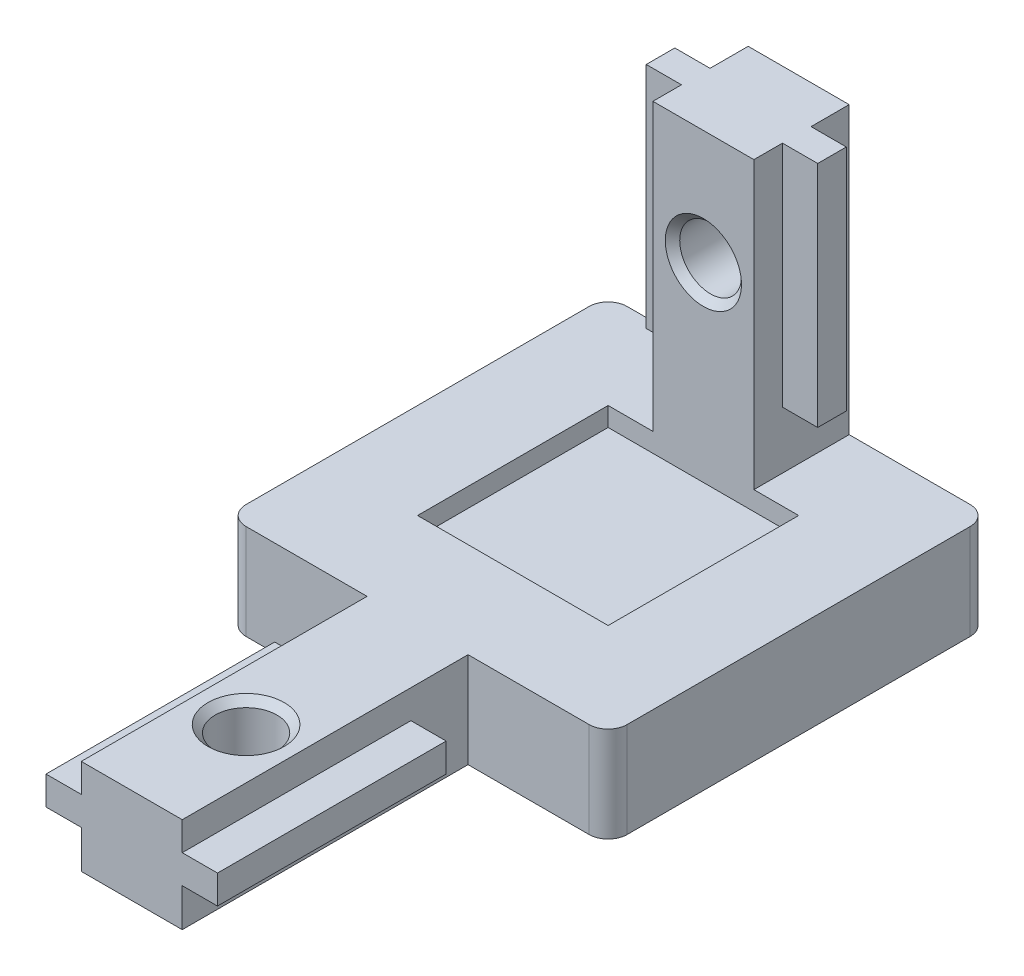
SolidWorks part; units mm, degrees
material "Stainless Steel (ferritic)"
ref_plane "Front Plane" through (0, 0, 0) normal (0, 0, 1) x (1, 0, 0)
ref_plane "Top Plane" through (0, 0, 0) normal (0, 1, 0) x (1, 0, 0)
ref_plane "Right Plane" through (0, 0, 0) normal (1, 0, 0) x (0, 0, -1)
ref_plane "Plane1" through (0, 5, 0) normal (0, 1, 0) x (1, 0, 0)
sketch "Sketch1" plane through (0, 5, 0) normal (0, 1, 0) x (1, 0, 0)
  line L0 (10, -35) -> (10, 0)
  line L1 (10, 0) -> (-10, 0)
  line L2 (-10, 0) -> (-10, -35)
  line L3 (-10, -35) -> (10, -35)
extrude "Boss-Extrude1" add sketch "Sketch1" against normal blind 5
sketch "Sketch2" plane through (0, 5, 0) normal (0, 1, 0) x (-1, 0, 0)
  line L0 (-2.65, 5) -> (2.65, 5)
  line L1 (2.65, 5) -> (2.65, 0)
  line L2 (2.65, 0) -> (-2.65, 0)
  line L3 (-2.65, 0) -> (-2.65, 5)
extrude "Boss-Extrude2" add sketch "Sketch2" along normal blind 15
sketch "Sketch3" plane through (0, 5, 0) normal (0, 1, 0) x (-1, 0, 0)
  line L0 (5, 15) -> (-5, 15)
  line L1 (-5, 15) -> (-5, 5)
  line L2 (-5, 5) -> (5, 5)
  line L3 (5, 5) -> (5, 15)
extrude "Cut-Extrude1" cut sketch "Sketch3" against normal blind 1
sketch "Sketch4" plane through (0, 0, 0) normal (0, -1, 0) x (1, 0, 0)
  line L0 (-10, 20) -> (-2.65, 20)
  line L1 (-2.65, 20) -> (-2.65, 35)
  line L2 (-2.65, 35) -> (-10, 35)
  line L3 (-10, 35) -> (-10, 20)
extrude "Cut-Extrude2" cut sketch "Sketch4" against normal through all
sketch "Sketch5" plane through (0, 0, 0) normal (0, -1, 0) x (1, 0, 0)
  line L0 (2.65, 35) -> (2.65, 20)
  line L1 (2.65, 20) -> (10, 20)
  line L2 (10, 20) -> (10, 35)
  line L3 (10, 35) -> (2.65, 35)
extrude "Cut-Extrude3" cut sketch "Sketch5" against normal through all
sketch "Sketch6" plane through (2.65, 0, 0) normal (1, 0, 0) x (0, 0, -1)
  line L0 (-2, 8) -> (-3.5, 8)
  line L1 (-3.5, 8) -> (-3.5, 20)
  line L2 (-3.5, 20) -> (-2, 20)
  line L3 (-2, 20) -> (-2, 8)
extrude "Boss-Extrude3" add sketch "Sketch6" along normal blind 1.85
sketch "Sketch7" plane through (-2.65, 0, 0) normal (-1, 0, 0) x (0, 0, 1)
  line L0 (3.5, 8) -> (2, 8)
  line L1 (2, 8) -> (2, 20)
  line L2 (2, 20) -> (3.5, 20)
  line L3 (3.5, 20) -> (3.5, 8)
extrude "Boss-Extrude4" add sketch "Sketch7" along normal blind 1.85
sketch "Sketch8" plane through (-2.65, 0, 0) normal (-1, 0, 0) x (0, 0, 1)
  line L0 (23, 2) -> (23, 3.5)
  line L1 (23, 3.5) -> (35, 3.5)
  line L2 (35, 3.5) -> (35, 2)
  line L3 (35, 2) -> (23, 2)
extrude "Boss-Extrude5" add sketch "Sketch8" along normal blind 1.85
sketch "Sketch9" plane through (2.65, 0, 0) normal (1, 0, 0) x (0, 0, -1)
  line L0 (-23, 3.5) -> (-23, 2)
  line L1 (-23, 2) -> (-35, 2)
  line L2 (-35, 2) -> (-35, 3.5)
  line L3 (-35, 3.5) -> (-23, 3.5)
extrude "Boss-Extrude6" add sketch "Sketch9" along normal blind 1.85
hole_wizard "M3 Clearance Hole1" positions "Sketch11" profile "Sketch10" hole size "M3" standard "ANSI Metric"
sketch "Sketch11" plane through (0, 0, 0) normal (0, -1, 0) x (-1, 0, 0)
  point P0 (0, -29)
sketch "Sketch10" plane through (0, 0, 29) normal (1, 0, 0) x (0, 0, -1)
  line L0 (0, 0) -> (0, 20)
  line L1 (0, 20) -> (1.621, 20)
  line L2 (1.621, 20) -> (1.621, 0)
  line L5 (1.621, 0) -> (0, 0)
  line L11 (0, -6.35) -> (0, 107.95) construction
  dimension "Thru Hole Dia." = 3.242
  dimension "Thru Hole Depth" = 20
hole_wizard "M3 Clearance Hole2" positions "Sketch13" profile "Sketch12" hole size "M3" standard "ANSI Metric"
sketch "Sketch13" plane through (0, 0, 5) normal (0, 0, 1) x (1, 0, 0)
  point P0 (0, 14)
sketch "Sketch12" plane through (0, 14, 5) normal (1, 0, 0) x (0, -1, 0)
  line L0 (0, 0) -> (0, 5.0001)
  line L1 (0, 5.0001) -> (1.621, 5.0001)
  line L2 (1.621, 5.0001) -> (1.621, 0)
  line L5 (1.621, 0) -> (0, 0)
  line L11 (0, -6.35) -> (0, 107.95) construction
  dimension "Thru Hole Dia." = 3.242
  dimension "Thru Hole Depth" = 5
chamfer "Chamfer1" distance 0.379 angle 45 4 edges at (0, 5, 30.621) (-1.621, 14, 0) (1.621, 14, 5) (0, 0, 27.379)
fillet "Fillet1" radius 1 4 edges at (-10, 2.5, 20) (10, 2.5, 0) (10, 2.5, 20) (-10, 2.5, 0)
